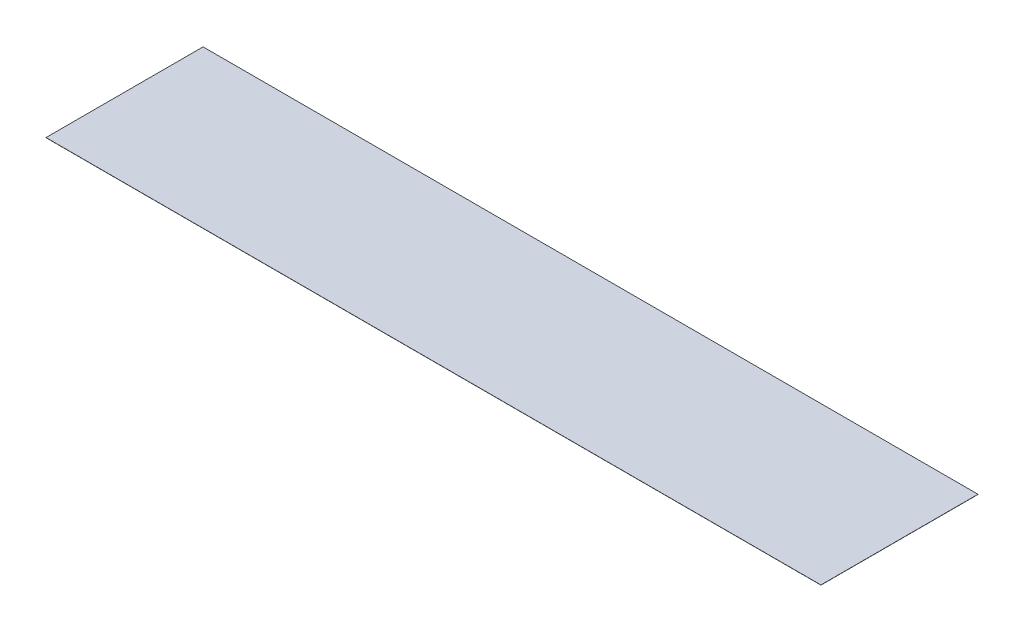
SolidWorks part; units mm, degrees
ref_plane "Front Plane" through (0, 0, 0) normal (0, 0, 1) x (1, 0, 0)
ref_plane "Top Plane" through (0, 0, 0) normal (0, 1, 0) x (1, 0, 0)
ref_plane "Right Plane" through (0, 0, 0) normal (1, 0, 0) x (0, 0, -1)
sketch "Sketch1" plane through (0, 0, 0) normal (0, 1, 0) x (1, 0, 0)
  line L1 (-11277.6, 0) -> (11277.6, 0)
  line L2 (-11277.6, 0) -> (-11277.6, 4572)
  line L3 (-11277.6, 4572) -> (11277.6, 4572)
  line L4 (11277.6, 0) -> (11277.6, 4572)
  point P5 (0, 0)
  dimension "D1" = 4572
  dimension "D2" = 22555.2
extrude "Boss-Extrude1" add sketch "Sketch1" along normal blind 4.7752
ref_plane "Plane1" through (0, 0, 0) normal (1, 0, 0) x (0, 0, -1)
